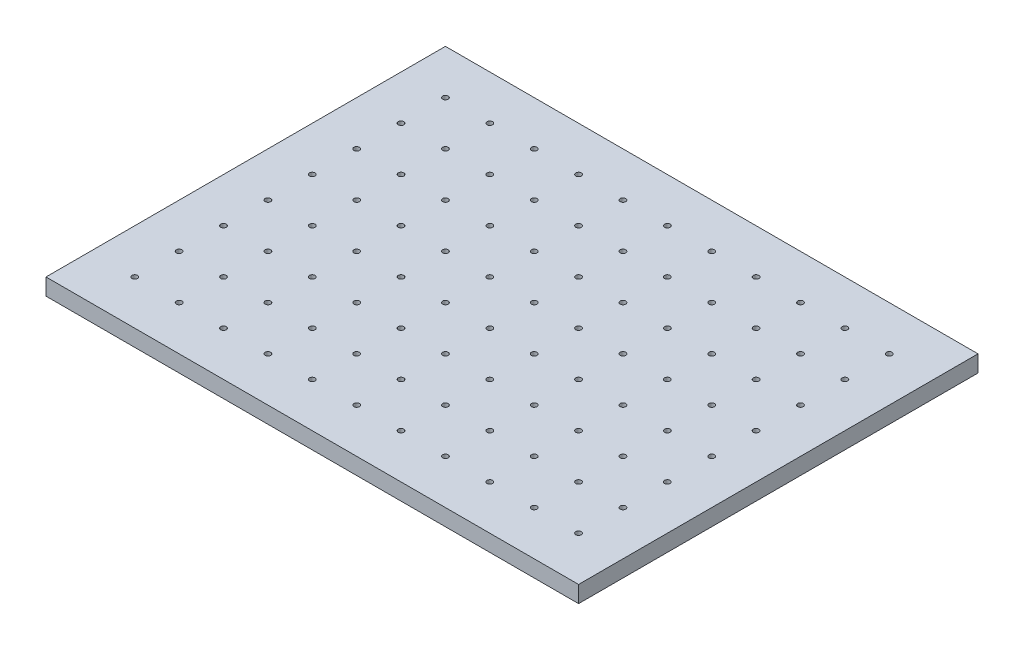
SolidWorks part; units mm, degrees
ref_plane "Front Plane" through (0, 0, 0) normal (0, 0, 1) x (1, 0, 0)
ref_plane "Top Plane" through (0, 0, 0) normal (0, 1, 0) x (1, 0, 0)
ref_plane "Right Plane" through (0, 0, 0) normal (1, 0, 0) x (0, 0, -1)
sketch "Sketch1" plane through (0, 0, 0) normal (0, 1, 0) x (1, 0, 0)
  line L1 (0, 0) -> (609.6, 0)
  line L2 (0, 0) -> (0, -457.2)
  line L3 (0, -457.2) -> (609.6, -457.2)
  line L4 (609.6, 0) -> (609.6, -457.2)
  circle A0 centre (50.8, -50.8) radius 3.175
  circle A1 centre (101.6, -50.8) radius 3.175
  circle A2 centre (152.4, -50.8) radius 3.175
  circle A3 centre (203.2, -50.8) radius 3.175
  circle A4 centre (254, -50.8) radius 3.175
  circle A5 centre (304.8, -50.8) radius 3.175
  circle A6 centre (355.6, -50.8) radius 3.175
  circle A7 centre (406.4, -50.8) radius 3.175
  circle A8 centre (457.2, -50.8) radius 3.175
  circle A9 centre (508, -50.8) radius 3.175
  circle A10 centre (558.8, -50.8) radius 3.175
  circle A11 centre (50.8, -101.6) radius 3.175
  circle A12 centre (101.6, -101.6) radius 3.175
  circle A13 centre (152.4, -101.6) radius 3.175
  circle A14 centre (203.2, -101.6) radius 3.175
  circle A15 centre (254, -101.6) radius 3.175
  circle A16 centre (304.8, -101.6) radius 3.175
  circle A17 centre (355.6, -101.6) radius 3.175
  circle A18 centre (406.4, -101.6) radius 3.175
  circle A19 centre (457.2, -101.6) radius 3.175
  circle A20 centre (508, -101.6) radius 3.175
  circle A21 centre (558.8, -101.6) radius 3.175
  circle A22 centre (50.8, -152.4) radius 3.175
  circle A23 centre (101.6, -152.4) radius 3.175
  circle A24 centre (152.4, -152.4) radius 3.175
  circle A25 centre (203.2, -152.4) radius 3.175
  circle A26 centre (254, -152.4) radius 3.175
  circle A27 centre (304.8, -152.4) radius 3.175
  circle A28 centre (355.6, -152.4) radius 3.175
  circle A29 centre (406.4, -152.4) radius 3.175
  circle A30 centre (457.2, -152.4) radius 3.175
  circle A31 centre (508, -152.4) radius 3.175
  circle A32 centre (558.8, -152.4) radius 3.175
  circle A33 centre (50.8, -203.2) radius 3.175
  circle A34 centre (101.6, -203.2) radius 3.175
  circle A35 centre (152.4, -203.2) radius 3.175
  circle A36 centre (203.2, -203.2) radius 3.175
  circle A37 centre (254, -203.2) radius 3.175
  circle A38 centre (304.8, -203.2) radius 3.175
  circle A39 centre (355.6, -203.2) radius 3.175
  circle A40 centre (406.4, -203.2) radius 3.175
  circle A41 centre (457.2, -203.2) radius 3.175
  circle A42 centre (508, -203.2) radius 3.175
  circle A43 centre (558.8, -203.2) radius 3.175
  circle A44 centre (50.8, -254) radius 3.175
  circle A45 centre (101.6, -254) radius 3.175
  circle A46 centre (152.4, -254) radius 3.175
  circle A47 centre (203.2, -254) radius 3.175
  circle A48 centre (254, -254) radius 3.175
  circle A49 centre (304.8, -254) radius 3.175
  circle A50 centre (355.6, -254) radius 3.175
  circle A51 centre (406.4, -254) radius 3.175
  circle A52 centre (457.2, -254) radius 3.175
  circle A53 centre (508, -254) radius 3.175
  circle A54 centre (558.8, -254) radius 3.175
  circle A55 centre (50.8, -304.8) radius 3.175
  circle A56 centre (101.6, -304.8) radius 3.175
  circle A57 centre (152.4, -304.8) radius 3.175
  circle A58 centre (203.2, -304.8) radius 3.175
  circle A59 centre (254, -304.8) radius 3.175
  circle A60 centre (304.8, -304.8) radius 3.175
  circle A61 centre (355.6, -304.8) radius 3.175
  circle A62 centre (406.4, -304.8) radius 3.175
  circle A63 centre (457.2, -304.8) radius 3.175
  circle A64 centre (508, -304.8) radius 3.175
  circle A65 centre (558.8, -304.8) radius 3.175
  circle A66 centre (50.8, -355.6) radius 3.175
  circle A67 centre (101.6, -355.6) radius 3.175
  circle A68 centre (152.4, -355.6) radius 3.175
  circle A69 centre (203.2, -355.6) radius 3.175
  circle A70 centre (254, -355.6) radius 3.175
  circle A71 centre (304.8, -355.6) radius 3.175
  circle A72 centre (355.6, -355.6) radius 3.175
  circle A73 centre (406.4, -355.6) radius 3.175
  circle A74 centre (457.2, -355.6) radius 3.175
  circle A75 centre (508, -355.6) radius 3.175
  circle A76 centre (558.8, -355.6) radius 3.175
  circle A77 centre (50.8, -406.4) radius 3.175
  circle A78 centre (101.6, -406.4) radius 3.175
  circle A79 centre (152.4, -406.4) radius 3.175
  circle A80 centre (203.2, -406.4) radius 3.175
  circle A81 centre (254, -406.4) radius 3.175
  circle A82 centre (304.8, -406.4) radius 3.175
  circle A83 centre (355.6, -406.4) radius 3.175
  circle A84 centre (406.4, -406.4) radius 3.175
  circle A85 centre (457.2, -406.4) radius 3.175
  circle A86 centre (508, -406.4) radius 3.175
  circle A87 centre (558.8, -406.4) radius 3.175
  dimension "D3" = 6.35
  dimension "D4" = 50.8
  dimension "D5" = 50.8
  dimension "D1" = 609.6
  dimension "D2" = 457.2
  dimension "D6" = 11
  dimension "D7" = 8
extrude "Boss-Extrude1" add sketch "Sketch1" along normal blind 19.05
